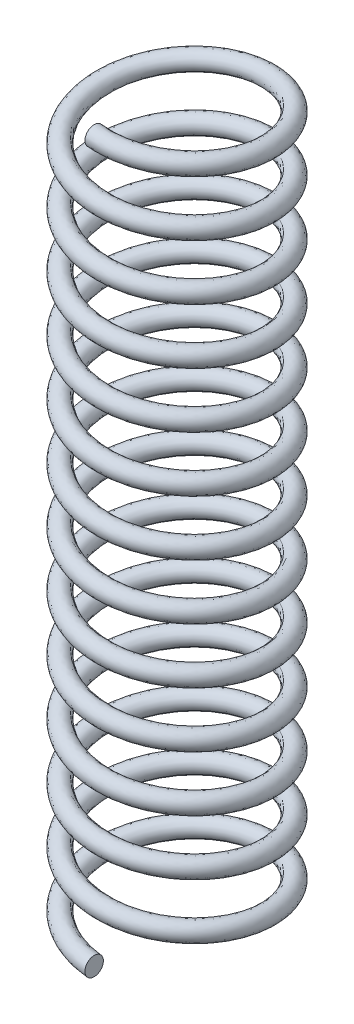
SolidWorks part; units mm, degrees
ref_plane "Front Plane" through (0, 0, 0) normal (0, 0, 1) x (1, 0, 0)
ref_plane "Top Plane" through (0, 0, 0) normal (0, 1, 0) x (1, 0, 0)
ref_plane "Right Plane" through (0, 0, 0) normal (1, 0, 0) x (0, 0, -1)
sketch "Sketch1" plane through (0, 0, 0) normal (0, 1, 0) x (1, 0, 0)
  circle A0 centre (0, 0) radius 28.575
  dimension "D1" = 57.15
curve "Helix/Spiral1" pitch 19.05 height 247.65 turns 13
sketch "Sketch2" plane through (0, 0, 0) normal (1, 0, 0) x (0, 0, -1)
  circle A0 centre (-28.5115, 0) radius 3.175
  dimension "D1" = 6.35
sweep "Sweep1" add profiles "Sketch2" path "Helix/Spiral1"
